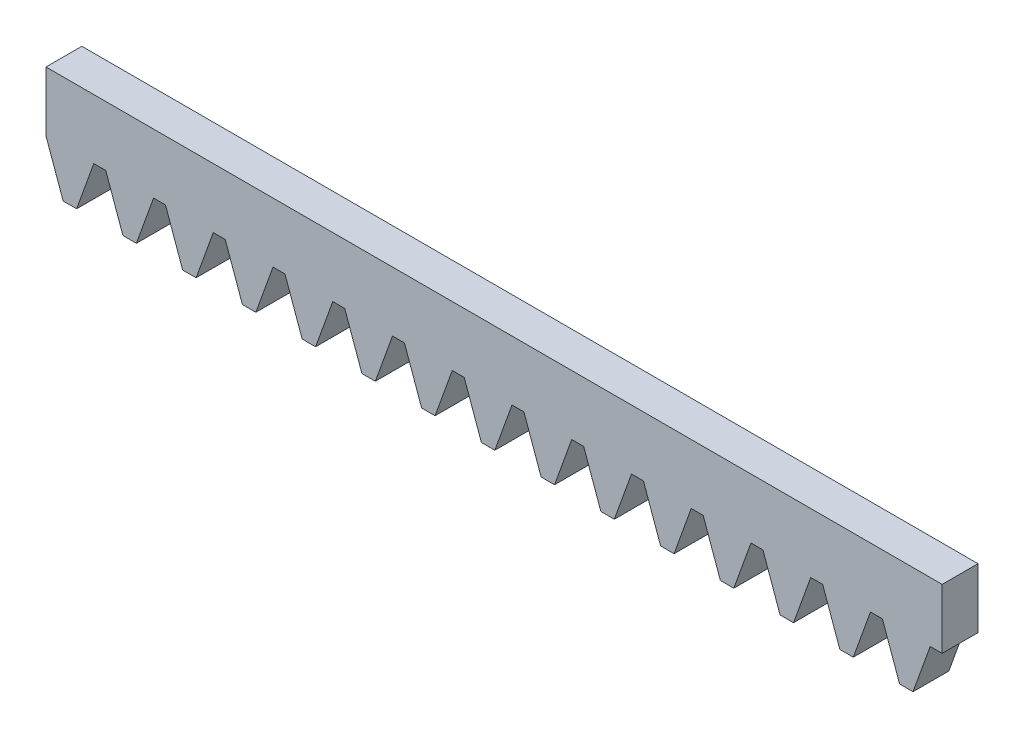
SolidWorks part; units mm, degrees
ref_plane "Front Plane" through (0, 0, 0) normal (0, 0, 1) x (1, 0, 0)
ref_plane "Top Plane" through (0, 0, 0) normal (0, 1, 0) x (1, 0, 0)
ref_plane "Right Plane" through (0, 0, 0) normal (1, 0, 0) x (0, 0, -1)
sketch "Sketch1" plane through (0, 0, 0) normal (0, 0, 1) x (1, 0, 0)
  line L1 (-75, -5) -> (75, -5)
  line L2 (-75, -5) -> (-75, 5)
  line L3 (-75, 5) -> (75, 5)
  line L4 (75, -5) -> (75, 5)
  line L5 (-75, -5) -> (75, 5) construction
  line L6 (-75, 5) -> (75, -5) construction
  line L9 (-67, -5) -> (-75, -5)
  line L17 (-72, -5) -> (-75, -5)
  line L21 (-62, -5) -> (-70, -5)
  line L25 (-52, -5) -> (-60, -5)
  line L29 (-42, -5) -> (-50, -5)
  line L33 (-32, -5) -> (-40, -5)
  line L37 (-22, -5) -> (-30, -5)
  line L41 (-12, -5) -> (-20, -5)
  line L45 (-2, -5) -> (-10, -5)
  line L49 (8, -5) -> (0, -5)
  line L53 (18, -5) -> (10, -5)
  line L57 (28, -5) -> (20, -5)
  line L61 (38, -5) -> (30, -5)
  line L65 (48, -5) -> (40, -5)
  line L69 (58, -5) -> (50, -5)
  line L73 (68, -5) -> (60, -5)
  line L77 (75, -5) -> (70, -5)
  point P0 (0, 0)
  dimension "D1" = 150
  dimension "D2" = 10
  dimension "D4" = 8
extrude "Boss-Extrude1" add sketch "Sketch1" along normal blind 6
sketch "Sketch2" plane through (0, 0, 6) normal (0, 0, 1) x (1, 0, 0)
  line L0 (-75, -5) -> (-72.125, -13)
  line L1 (-72.125, -13) -> (-69.875, -13)
  line L2 (-69.875, -13) -> (-67, -5)
  line L3 (-67, -5) -> (-75, -5)
  line L5 (-75, -5) -> (75, -5) construction
  line L6 (-75, -5) -> (-75, 5) construction
  point P7 (0, 0)
  point P9 (0, 0)
  dimension "D1" = 8
  dimension "D2" = 2.25
  dimension "D3" = 8
  dimension "D4" = 109.767
extrude "Boss-Extrude2" add sketch "Sketch2" against normal up to surface (6 mm away) up to face at (0, 0, 0)
pattern_linear "LPattern1" count 15 spacing 10 along (1, 0, 0) of "Boss-Extrude2"
